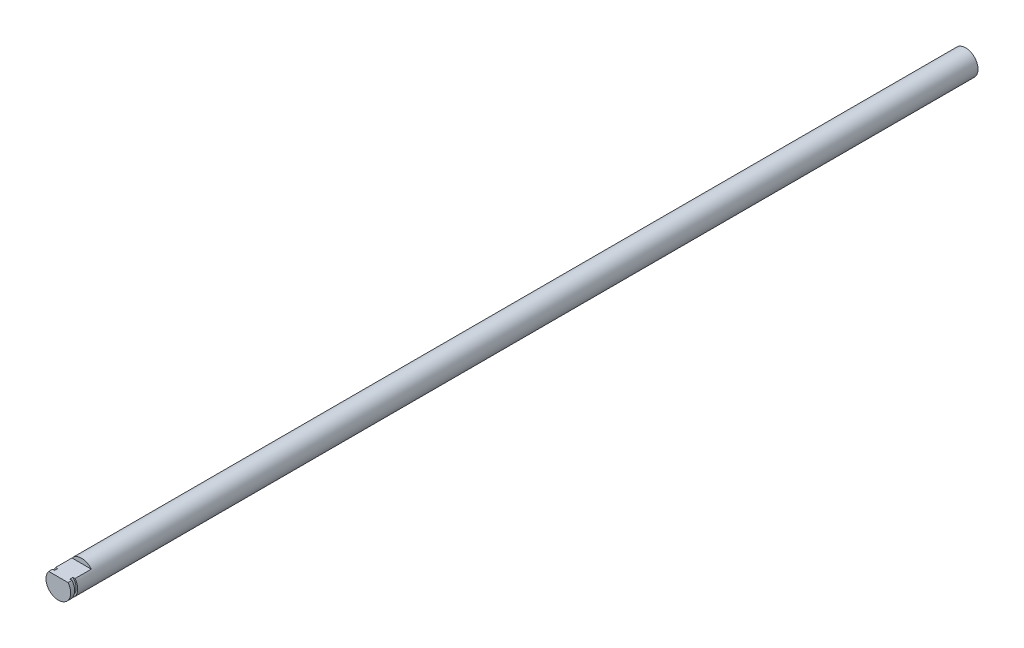
SolidWorks part; units mm, degrees
ref_plane "Front Plane" through (0, 0, 0) normal (0, 0, 1) x (1, 0, 0)
ref_plane "Top Plane" through (0, 0, 0) normal (0, 1, 0) x (1, 0, 0)
ref_plane "Right Plane" through (0, 0, 0) normal (1, 0, 0) x (0, 0, -1)
sketch "Sketch1" plane through (0, 0, 0) normal (0, 0, 1) x (1, 0, 0)
  circle A0 centre (0, 0) radius 4
  dimension "D1" = 8
extrude "Boss-Extrude1" add sketch "Sketch1" along normal blind 325
sketch "Sketch2" plane through (0, 0, 325) normal (0, 0, 1) x (1, 0, 0)
  line L0 (3.1225, 2.5) -> (-3.1225, 2.5)
  circle A1 centre (0, 0) radius 4
  arc A2 (3.1225, 2.5) -> (-3.1225, 2.5) centre (0, 0) ccw
  dimension "D2" = 2.5
  dimension "D1" = 0
extrude "Cut-Extrude1" cut sketch "Sketch2" against normal blind 7.5
ref_plane "Plane1" through (0, 0, 323.75) normal (0, 0, 1) x (1, 0, 0)
sketch "Sketch3" plane through (0, 0, 323.75) normal (0, 0, 1) x (1, 0, 0)
  circle A0 centre (0, 0) radius 4
  circle A1 centre (0, 0) radius 3.5
extrude "Cut-Extrude2" cut sketch "Sketch3" against normal blind 1
sketch "Sketch5" plane through (0, 0, 0) normal (0, 0, -1) x (-1, 0, 0)
  circle A1 centre (0, 0) radius 4
  circle A2 centre (0, 0) radius 4
  dimension "D1" = 0
extrude "Cut-Extrude3" cut sketch "Sketch5" against normal blind 65
sketch "Sketch6" plane through (0, 0, 65) normal (0, 0, -1) x (-1, 0, 0)
  circle A1 centre (0, 0) radius 4
  circle A2 centre (0, 0) radius 4
  dimension "D1" = 0
extrude "Boss-Extrude2" add sketch "Sketch6" along normal blind 13
sketch "Sketch7" plane through (0, 0, 52) normal (0, 0, -1) x (-1, 0, 0)
  circle A1 centre (0, 0) radius 4
  circle A2 centre (0, 0) radius 4
  dimension "D1" = 0
extrude "Boss-Extrude3" add sketch "Sketch7" along normal blind 10
sketch "Sketch8" plane through (0, 0, 42) normal (0, 0, -1) x (-1, 0, 0)
  circle A1 centre (0, 0) radius 4
  circle A2 centre (0, 0) radius 4
  dimension "D1" = 0
extrude "Boss-Extrude4" add sketch "Sketch8" along normal blind 40
sketch "Sketch9" plane through (0, 0, 2) normal (0, 0, -1) x (-1, 0, 0)
  circle A1 centre (0, 0) radius 4
  circle A2 centre (0, 0) radius 4
  dimension "D1" = 0
extrude "Cut-Extrude4" cut sketch "Sketch9" against normal blind 30
